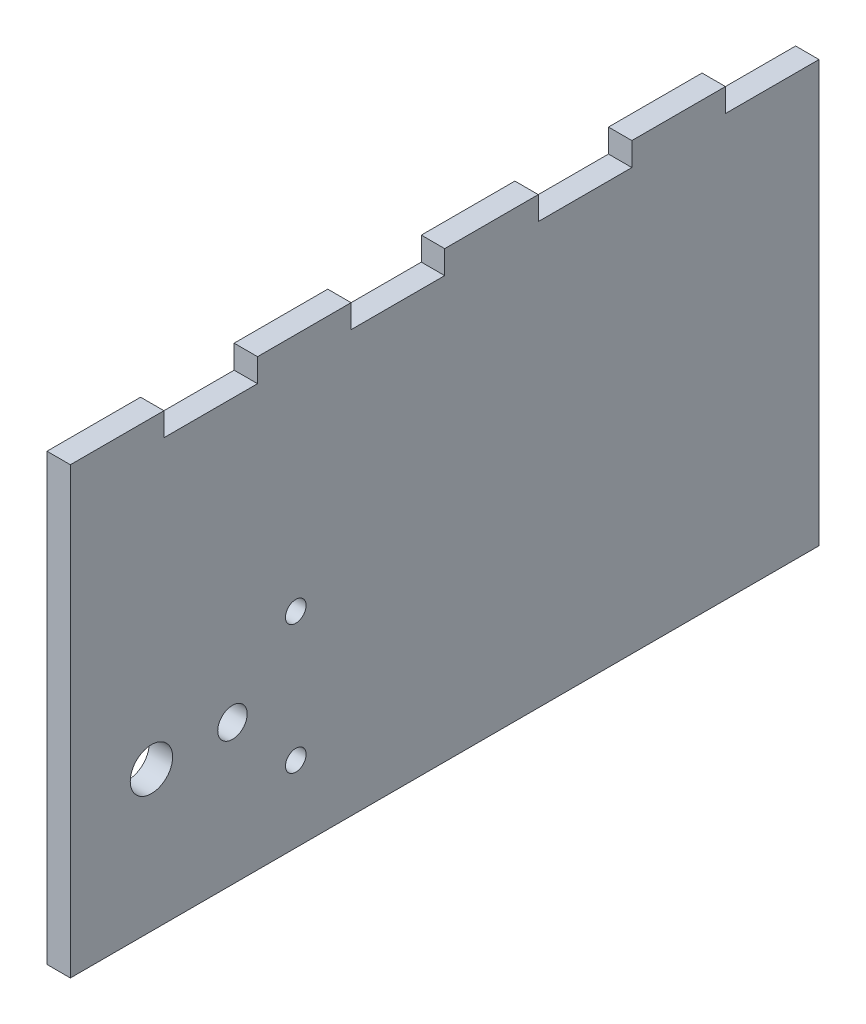
SolidWorks part; units mm, degrees
ref_plane "Front Plane" through (0, 0, 0) normal (0, 0, 1) x (1, 0, 0)
ref_plane "Top Plane" through (0, 0, 0) normal (0, 1, 0) x (1, 0, 0)
ref_plane "Right Plane" through (0, 0, 0) normal (1, 0, 0) x (0, 0, -1)
sketch "Sketch1" plane through (0, 0, 0) normal (1, 0, 0) x (0, 0, -1)
  line L0 (0, 0) -> (0, 60.325)
  line L1 (0, 60.325) -> (12.7, 60.325)
  line L2 (12.7, 57.15) -> (25.4, 57.15)
  line L3 (25.4, 57.15) -> (25.4, 60.325)
  line L4 (25.4, 60.325) -> (38.1, 60.325)
  line L5 (38.1, 60.325) -> (38.1, 57.15)
  line L6 (38.1, 57.15) -> (50.8, 57.15)
  line L7 (50.8, 57.15) -> (50.8, 60.325)
  line L8 (50.8, 60.325) -> (63.5, 60.325)
  line L9 (63.5, 60.325) -> (63.5, 57.15)
  line L10 (63.5, 57.15) -> (76.2, 57.15)
  line L11 (76.2, 57.15) -> (76.2, 60.325)
  line L12 (76.2, 60.325) -> (88.9, 60.325)
  line L13 (88.9, 60.325) -> (88.9, 57.15)
  line L14 (88.9, 57.15) -> (101.6, 57.15)
  line L15 (101.6, 57.15) -> (101.6, 0)
  line L16 (101.6, 0) -> (0, 0)
  line L17 (12.7, 60.325) -> (12.7, 57.15)
  dimension "D1" = 101.6
  dimension "D2" = 3.175
  dimension "D10" = 57.15
extrude "Boss-Extrude1" add sketch "Sketch1" along normal blind 3.175
sketch "Sketch2" plane through (3.175, 0, 0) normal (1, 0, 0) x (0, 0, -1)
  line L0 (11, 19.05) -> (30.591, 19.05) construction
  line L1 (0, 60.325) -> (0, 0) construction
  line L2 (50.8, 60.325) -> (50.8, 0) construction
  line L3 (0, 0) -> (101.6, 0) construction
  line L4 (30.591, 27.8) -> (30.591, 10.3) construction
  circle A4 centre (30.591, 10.3) radius 1.4
  circle A5 centre (30.591, 27.8) radius 1.4
  circle A6 centre (22, 19.05) radius 2
  circle A7 centre (11, 19.05) radius 2.877
  dimension "D2" = 4
  dimension "D3" = 2.8
  dimension "D1" = 5.754
  dimension "D4" = 2.8
  dimension "D8" = 11
  dimension "D5" = 11
  dimension "D6" = 19.591
  dimension "D7" = 19.05
  dimension "D10" = 17.5
  dimension "D11" = 8.75
extrude "Cut-Extrude1" cut sketch "Sketch2" against normal up to next
